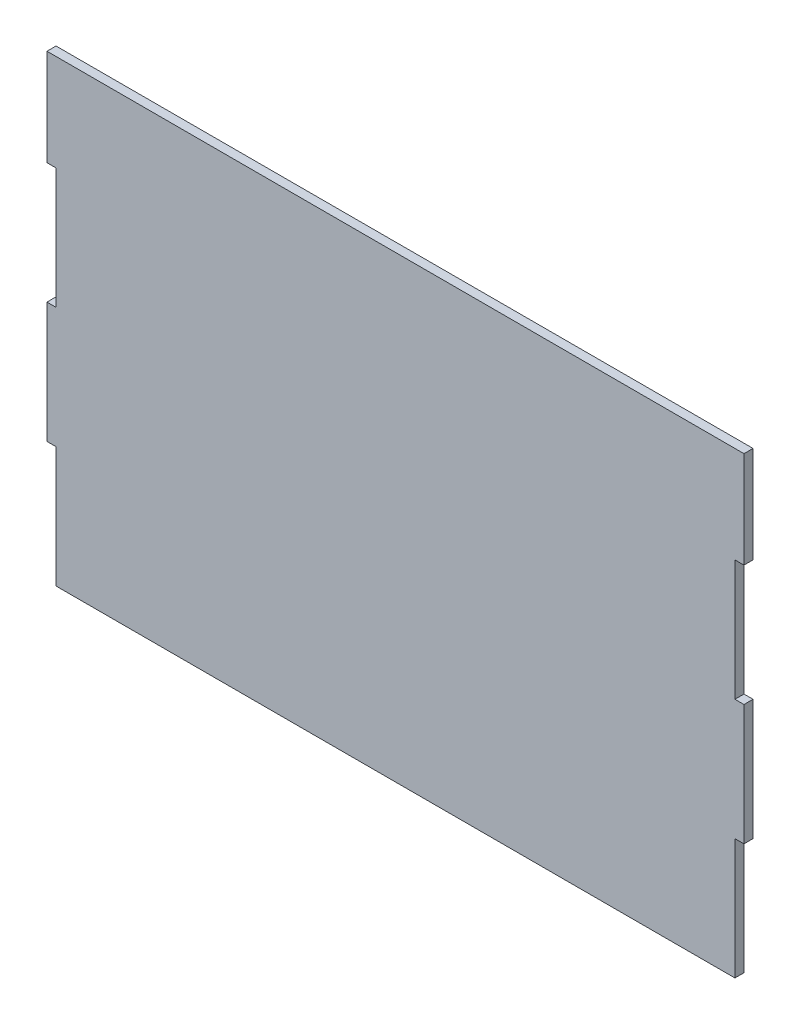
SolidWorks part; units mm, degrees
ref_plane "Front Plane" through (0, 0, 0) normal (0, 0, 1) x (1, 0, 0)
ref_plane "Top Plane" through (0, 0, 0) normal (0, 1, 0) x (1, 0, 0)
ref_plane "Right Plane" through (0, 0, 0) normal (1, 0, 0) x (0, 0, -1)
sketch "Sketch1" plane through (0, 0, 0) normal (0, 0, 1) x (1, 0, 0)
  line L0 (-112.5, 20) -> (-115.5, 20)
  line L2 (-112.5, 60) -> (-112.5, 20)
  line L3 (-112.5, -60) -> (112.5, -60)
  line L4 (112.5, 60) -> (112.5, 20)
  line L5 (-112.5, 60) -> (112.5, -60) construction
  line L6 (-112.5, -60) -> (112.5, 60) construction
  line L7 (-115.5, 20) -> (-115.5, -20)
  line L8 (-115.5, -20) -> (-112.5, -20)
  line L9 (-112.5, -20) -> (-112.5, -60)
  line L10 (112.5, 20) -> (115.5, 20)
  line L11 (115.5, 20) -> (115.5, -20)
  line L12 (115.5, -20) -> (112.5, -20)
  line L13 (112.5, -20) -> (112.5, -60)
  line L15 (-112.5, 92) -> (112.5, 92)
  line L17 (-112.5, 60) -> (-115.5, 60)
  line L18 (-115.5, 60) -> (-115.5, 92)
  line L19 (-115.5, 92) -> (-112.5, 92)
  line L20 (112.5, 92) -> (115.5, 92)
  line L21 (115.5, 92) -> (115.5, 60)
  line L22 (115.5, 60) -> (112.5, 60)
  point P0 (0, 0)
  dimension "D1" = 120
  dimension "D2" = 225
  dimension "D3" = 40
  dimension "D4" = 32
  dimension "D5" = 3
  dimension "D6" = 225
  dimension "D7" = 40
  dimension "D8" = 3
extrude "Boss-Extrude1" add sketch "Sketch1" along normal blind 3
